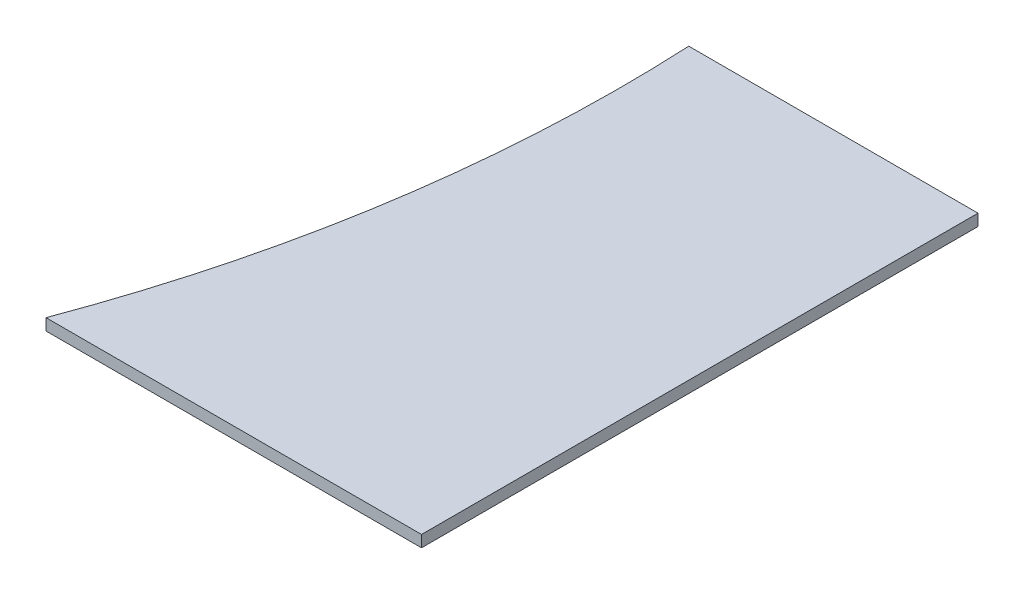
SolidWorks part; units mm, degrees
ref_plane "Front Plane" through (0, 0, 0) normal (0, 0, 1) x (1, 0, 0)
ref_plane "Top Plane" through (0, 0, 0) normal (0, 1, 0) x (1, 0, 0)
ref_plane "Right Plane" through (0, 0, 0) normal (1, 0, 0) x (0, 0, -1)
sketch "Sketch2" plane through (0, 0, 0) normal (0, 1, 0) x (1, 0, 0)
  line L0 (-39.37, 76.2) -> (-39.8465, 76.2)
  line L1 (-39.37, -76.2) -> (39.37, -76.2)
  line L3 (-39.37, 76.2) -> (39.37, 76.2)
  line L4 (39.37, -76.2) -> (39.37, 76.2)
  line L5 (-39.37, -76.2) -> (39.37, 76.2) construction
  line L6 (-39.37, 76.2) -> (39.37, -76.2) construction
  line L7 (-39.37, -76.2) -> (-63.4684, -76.2)
  arc A0 (-63.4684, -76.2) -> (-39.8465, 76.2) centre (-420.37, 57.15) ccw
  point P0 (0, 0)
  dimension "D3" = 762
  dimension "D4" = 420.37
  dimension "D1" = 152.4
  dimension "D2" = 78.74
  dimension "D5" = 57.15
extrude "Boss-Extrude2" add sketch "Sketch2" along normal blind 3.175
